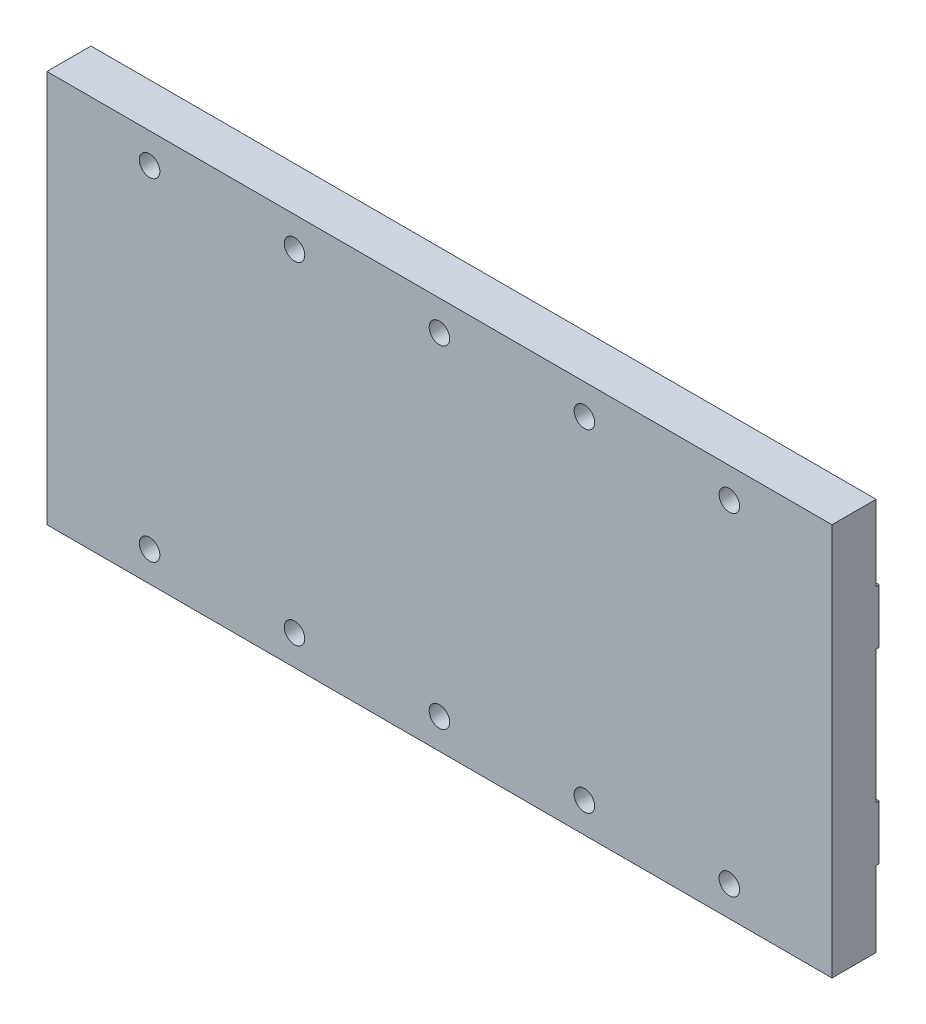
SolidWorks part; units mm, degrees
ref_plane "Plan de face" through (0, 0, 0) normal (0, 0, 1) x (1, 0, 0)
ref_plane "Plan de dessus" through (0, 0, 0) normal (0, 1, 0) x (1, 0, 0)
ref_plane "Plan de droite" through (0, 0, 0) normal (1, 0, 0) x (0, 0, -1)
sketch "Esquisse1" plane through (0, 0, 0) normal (0, 0, 1) x (1, 0, 0)
  line L1 (0, 0) -> (130, 0)
  line L2 (0, 0) -> (0, 65)
  line L3 (0, 65) -> (130, 65)
  line L4 (130, 0) -> (130, 65)
  circle A0 centre (113, 5) radius 1.3
  circle A1 centre (89, 5) radius 1.3
  circle A2 centre (65, 5) radius 1.3
  circle A3 centre (41, 5) radius 1.3
  circle A4 centre (17, 5) radius 1.3
  circle A5 centre (113, 60) radius 1.3
  circle A6 centre (89, 60) radius 1.3
  circle A7 centre (65, 60) radius 1.3
  circle A8 centre (41, 60) radius 1.3
  circle A9 centre (17, 60) radius 1.3
  dimension "D3" = 17
  dimension "D14" = 17
  dimension "D1" = 130
  dimension "D2" = 65
  dimension "D4" = 24
  dimension "D5" = 24
  dimension "D6" = 24
  dimension "D7" = 24
  dimension "D8" = 5
  dimension "D9" = 5
  dimension "D10" = 5
  dimension "D11" = 5
  dimension "D12" = 5
  dimension "D13" = 17
  dimension "D15" = 24
  dimension "D16" = 24
  dimension "D17" = 24
  dimension "D18" = 24
  dimension "D19" = 5
  dimension "D20" = 5
  dimension "D21" = 5
  dimension "D22" = 5
  dimension "D23" = 5
extrude "Boss.-Extru.1" add sketch "Esquisse1" along normal blind 7.8
sketch "Esquisse2" plane through (0, 0, 0) normal (0, 0, -1) x (-1, 0, 0)
  line L0 (0, 65) -> (0, 0) construction
  line L1 (-130, 65) -> (0, 65)
  line L2 (-130, 65) -> (-130, 52.5)
  line L3 (-130, 52.5) -> (0, 52.5)
  line L4 (0, 65) -> (0, 52.5)
  line L5 (-130, 0) -> (-130, 65) construction
  line L6 (0, 0) -> (-130, 0)
  line L7 (0, 0) -> (0, 12.5)
  line L8 (0, 12.5) -> (-130, 12.5)
  line L9 (-130, 0) -> (-130, 12.5)
  line L11 (-130, 43.5) -> (0, 43.5)
  line L12 (-130, 43.5) -> (-130, 21.5)
  line L13 (-130, 21.5) -> (0, 21.5)
  line L14 (0, 43.5) -> (0, 21.5)
  dimension "D1" = 12.5
  dimension "D2" = 9
  dimension "D3" = 9
  dimension "D4" = 12.5
extrude "Enlèv. mat.-Extru.1" cut sketch "Esquisse2" against normal blind 0.5
hole_wizard "Dégagement M3" positions "Esquisse3" profile "Esquisse4" hole size "M3" standard "ISO"
sketch "Esquisse3" plane through (0, 0, 7.8) normal (0, 0, 1) x (1, 0, 0)
  point P0 (17, 60)
  point P3 (41, 60)
  point P6 (65, 60)
  point P9 (89, 60)
  point P12 (113, 60)
  point P15 (113, 5)
  point P18 (89, 5)
  point P21 (65, 5)
  point P24 (41, 5)
  point P27 (17, 5)
sketch "Esquisse4" plane through (17, 60, 7.8) normal (1, 0, 0) x (0, -1, 0)
  line L0 (0, 0) -> (0, 8)
  line L1 (0, 8) -> (1.7, 6.9785)
  line L2 (1.7, 6.9785) -> (1.7, 0)
  line L5 (1.7, 0) -> (0, 0)
  line L10 (0, 8) -> (-1.7, 6.9785) construction
  line L11 (0, -6.35) -> (0, 107.95) construction
  dimension "Diamètre du perçage" = 3.4
  dimension "Profondeur du perçage" = 8
  dimension "Angle de pointe" = 118
